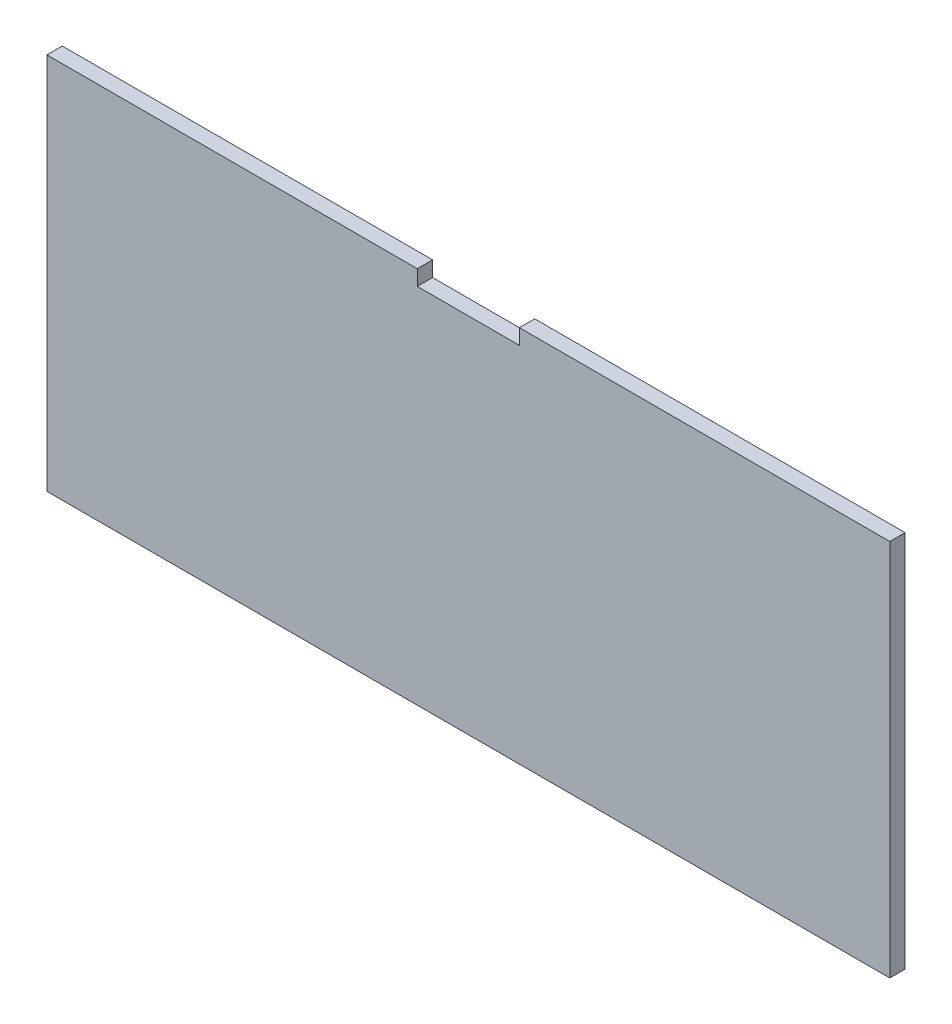
SolidWorks part; units mm, degrees
ref_plane "Plano frontal" through (0, 0, 0) normal (0, 0, 1) x (1, 0, 0)
ref_plane "Plano superior" through (0, 0, 0) normal (0, 1, 0) x (1, 0, 0)
ref_plane "Plano direito" through (0, 0, 0) normal (1, 0, 0) x (0, 0, -1)
sketch "Esboço3" plane through (0, 0, 0) normal (0, 0, 1) x (1, 0, 0)
  line L0 (-85.8613, 19.5271) -> (79.1387, 19.5271)
  line L1 (-85.8613, 19.5271) -> (-85.8613, -54.4729)
  line L2 (-85.8613, -54.4729) -> (79.1387, -54.4729)
  line L3 (79.1387, 19.5271) -> (79.1387, -54.4729)
  line L4 (-13.3613, 19.5271) -> (6.6387, 19.5271)
  line L5 (-13.3613, 19.5271) -> (-13.3613, 16.5271)
  line L6 (-13.3613, 16.5271) -> (6.6387, 16.5271)
  line L7 (6.6387, 19.5271) -> (6.6387, 16.5271)
  dimension "D1" = 74
  dimension "D2" = 74
  dimension "D3" = 165
  dimension "D4" = 0
  dimension "D5" = 20
  dimension "D6" = 72.5
  dimension "D7" = 72.5
extrude "Ressalto-extrusão1" add sketch "Esboço3" against normal blind 3 contours L0 L7 L6 L5 L1 L2 L3
